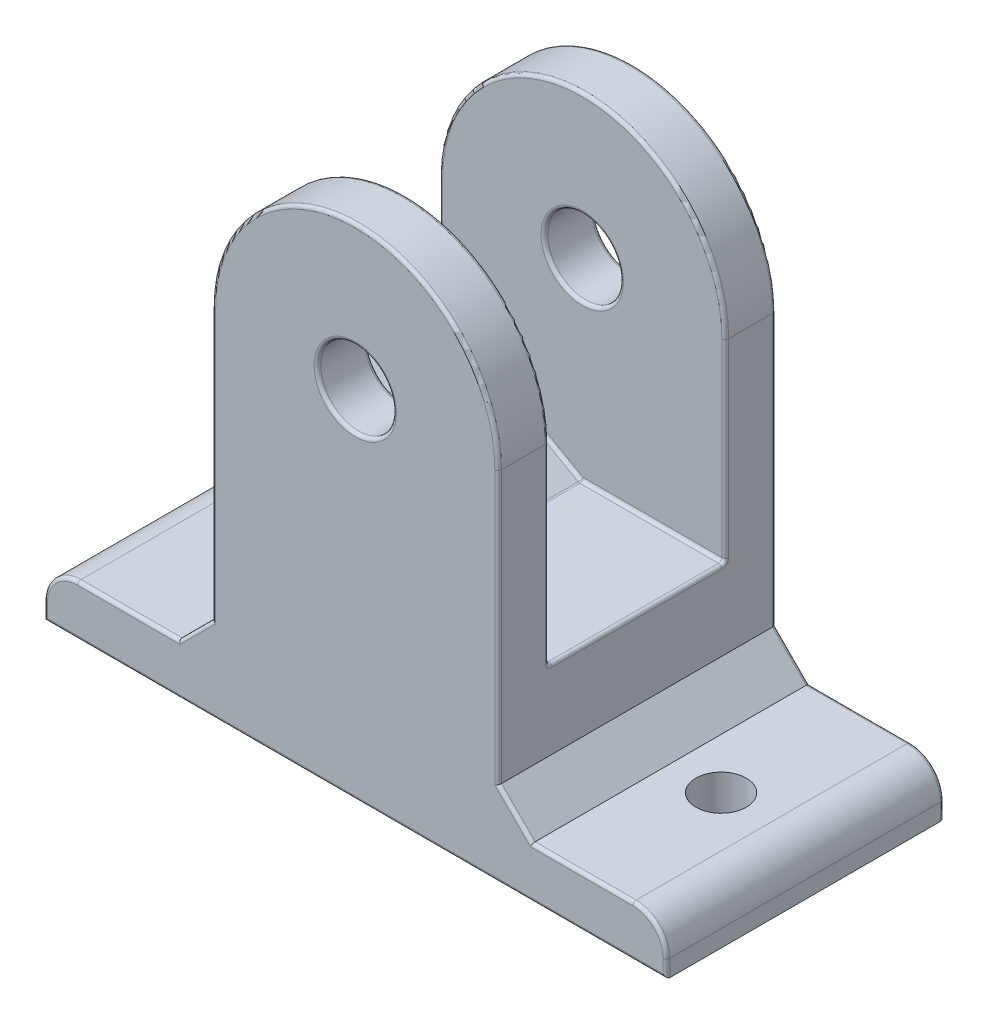
SolidWorks part; units mm, degrees
ref_plane "Front Plane" through (0, 0, 0) normal (0, 0, 1) x (1, 0, 0)
ref_plane "Top Plane" through (0, 0, 0) normal (0, 1, 0) x (1, 0, 0)
ref_plane "Right Plane" through (0, 0, 0) normal (1, 0, 0) x (0, 0, -1)
sketch "Sketch1" plane through (0, 0, 0) normal (0, 0, 1) x (1, 0, 0)
  line L0 (8.5, 21.15) -> (8.5, 0)
  line L1 (0, 0) -> (0, 21.15) construction
  line L2 (-8.5, 21.15) -> (-8.5, 0)
  line L3 (8.5, 0) -> (-8.5, 0)
  circle A0 centre (0, 21.15) radius 2.25
  arc A2 (-8.5, 21.15) -> (8.5, 21.15) centre (0, 21.15) cw
extrude "Boss-Extrude1" add sketch "Sketch1" along normal blind 3
ref_plane "Plane1" through (0, 0, 0) normal (0, 0, -1) x (-1, 0, 0)
sketch "Sketch2" plane through (0, 0, 0) normal (0, 0, -1) x (-1, 0, 0)
  line L0 (-8.5, 9.6849) -> (0, 9.6849)
  line L1 (-8.5, 0) -> (-8.5, 21.15) construction
  line L2 (0, 9.6849) -> (8.5, 14.5162)
  line L3 (8.5, 21.15) -> (8.5, 0) construction
  line L4 (8.5, 14.5162) -> (8.5, 0)
  line L5 (8.5, 0) -> (-8.5, 0)
  line L6 (-8.5, 0) -> (-8.5, 9.6849)
  point P0 (-8.5, 9.6849)
extrude "Boss-Extrude2" add sketch "Sketch2" along normal blind 10.5
ref_plane "Plane2" through (0, 0, -10.5) normal (0, 0, -1) x (-1, 0, 0)
sketch "Sketch3" plane through (0, 0, -10.5) normal (0, 0, -1) x (-1, 0, 0)
  line L0 (-8.5, 21.15) -> (-8.5, 0)
  line L1 (-8.5, 0) -> (8.5, 0)
  line L2 (8.5, 0) -> (8.5, 21.15)
  arc A0 (-8.5, 21.15) -> (8.5, 21.15) centre (0, 21.15) cw
  arc A1 (8.5, 21.15) -> (-8.5, 21.15) centre (0, 21.15) ccw construction
  circle A2 centre (0, 21.15) radius 2.25
extrude "Boss-Extrude3" add sketch "Sketch3" along normal blind 3
sketch "Sketch4" plane through (0, 0, 0) normal (0, 1, 0) x (1, 0, 0)
  line L0 (8.5, 13.5) -> (8.5, -3) construction
  line L1 (8.5, -3) -> (-14.2453, -3) construction
  line L2 (0, 0) -> (0, 16.0892) construction
  line L3 (8.5, 13.5) -> (18.5, 13.5)
  line L4 (8.5, 13.5) -> (8.5, -3)
  line L5 (8.5, -3) -> (18.5, -3)
  line L6 (18.5, 13.5) -> (18.5, -3)
  line L7 (18.5, 13.5) -> (8.5, -3) construction
  line L8 (8.5, 13.5) -> (18.5, -3) construction
  line L9 (18.5, -3) -> (18.3749, -3.1514) construction
  line L10 (-18.5, -3) -> (-18.3749, -3.1514) construction
  line L11 (-8.5, 13.5) -> (-18.5, -3) construction
  line L12 (-18.5, 13.5) -> (-8.5, -3) construction
  line L13 (-8.5, 13.5) -> (-8.5, -3) construction
  line L14 (-18.5, 13.5) -> (-18.5, -3)
  line L15 (-8.5, -3) -> (-18.5, -3)
  line L16 (-8.5, 13.5) -> (-8.5, -3)
  line L17 (-8.5, 13.5) -> (-18.5, 13.5)
  circle A0 centre (13.5, 5.25) radius 1.5
  circle A1 centre (-13.5, 5.25) radius 1.5
extrude "Boss-Extrude4" add sketch "Sketch4" along normal blind 3
chamfer "Chamfer1" distance 2 angle 45 2 edges at (-8.5, 3, -5.25) (8.5, 3, -5.25)
fillet "Fillet1" radius 2 2 edges at (-18.5, 3, -5.25) (18.5, 3, -5.25)
fillet "Fillet2" radius 0.2 41 edges at (8.5, 9.6849, -5.25) (-8.5, 14.5162, -5.25) (-2.25, 21.15, -10.5) (0, 29.65, -10.5) (8.5, 15.4174, -10.5) (4.25, 9.6849, -10.5) (-4.25, 12.1005, -10.5) (-8.5, 17.8331, -10.5) (2.25, 21.15, 0) (8.5, 15.4174, 0) (0, 29.65, 0) (-8.5, 17.8331, 0) (-4.25, 12.1005, 0) (4.25, 9.6849, 0) (2.25, 21.15, 3) (-9.5, 4, 3) (-8.5, 13.075, 3) (0, 29.65, 3) (8.5, 13.075, 3) (9.5, 4, 3) (13.5, 3, 3) (17.9142, 2.4142, 3) (18.5, 0.5, 3) (0, 0, 3) (-18.5, 0.5, 3) (-17.9142, 2.4142, 3) (-13.5, 3, 3) (-2.25, 21.15, -13.5) (0, 0, -13.5) (18.5, 0.5, -13.5) (17.9142, 2.4142, -13.5) (13.5, 3, -13.5) (9.5, 4, -13.5) (8.5, 13.075, -13.5) (0, 29.65, -13.5) (-8.5, 13.075, -13.5) (-9.5, 4, -13.5) (-13.5, 3, -13.5) (-17.9142, 2.4142, -13.5) (-18.5, 0.5, -13.5) (0, 9.6849, -5.25)
